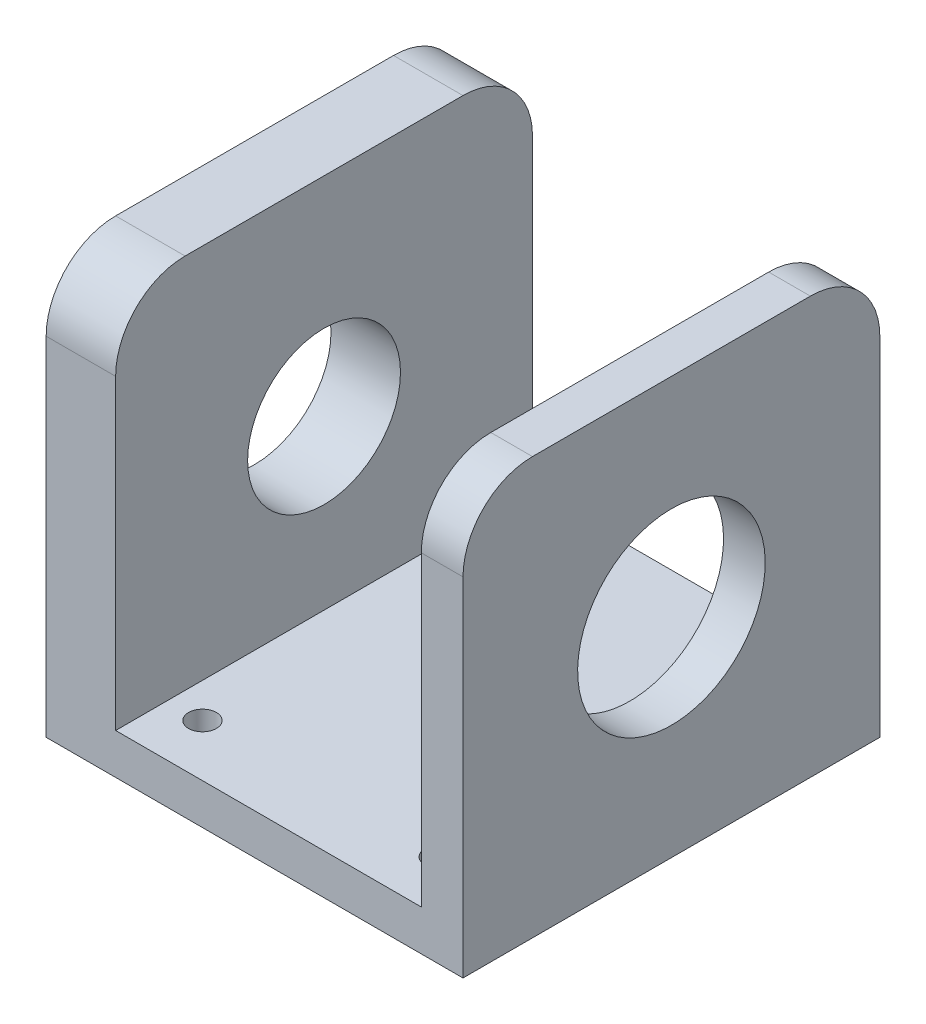
SolidWorks part; units mm, degrees
ref_plane "Front Plane" through (0, 0, 0) normal (0, 0, 1) x (1, 0, 0)
ref_plane "Top Plane" through (0, 0, 0) normal (0, 1, 0) x (1, 0, 0)
ref_plane "Right Plane" through (0, 0, 0) normal (1, 0, 0) x (0, 0, -1)
sketch "Sketch1" plane through (0, 0, 0) normal (0, 0, 1) x (1, 0, 0)
  line L0 (-30, 30) -> (-30, -30)
  line L1 (-30, -30) -> (30, -30)
  line L2 (30, -30) -> (30, 30)
  line L3 (-20, 30) -> (-20, -24.1479)
  line L4 (-20, -24.1479) -> (24, -24.1479)
  line L5 (24, -24.1479) -> (24, 30)
  line L6 (-30, 30) -> (-20, 30)
  line L7 (24, 30) -> (30, 30)
  point P3 (0, -30)
  point P6 (-30, 0)
  dimension "D1" = 60
  dimension "D2" = 60
  dimension "D3" = 60
  dimension "D5" = 6
  dimension "D4" = 10
  dimension "D6" = 44
extrude "Boss-Extrude1" add sketch "Sketch1" along normal mid plane 60
sketch "Sketch2" plane through (0, 0, 0) normal (1, 0, 0) x (0, 0, -1)
  circle A0 centre (0, 0) radius 11
  dimension "D1" = 22
extrude "Cut-Extrude1" cut sketch "Sketch2" against normal blind 60
fillet "Fillet1" radius 10 4 edges at (27, 30, 30) (27, 30, -30) (-25, 30, -30) (-25, 30, 30)
sketch "Sketch3" plane through (0, -24.1479, 0) normal (0, 1, 0) x (1, 0, 0)
  line L0 (-20, -30) -> (-20, 30) construction
  line L1 (-15, -22.5) -> (19, -22.5) construction
  line L2 (-15, -22.5) -> (-15, 22.5) construction
  line L3 (-15, 22.5) -> (19, 22.5) construction
  line L4 (19, -22.5) -> (19, 22.5) construction
  line L5 (-15, -22.5) -> (19, 22.5) construction
  line L6 (-15, 22.5) -> (19, -22.5) construction
  line L8 (24, -20) -> (24, 20) construction
  circle A0 centre (-15, 22.5) radius 2
  circle A1 centre (19, 22.5) radius 2
  circle A2 centre (-15, -22.5) radius 2
  circle A3 centre (19, -22.5) radius 2
  point P0 (0, 0)
  point P10 (0, 0)
  dimension "D3" = 4
  dimension "D4" = 4
  dimension "D5" = 4
  dimension "D6" = 4
  dimension "D1" = 45
  dimension "D2" = 5
  dimension "D7" = 5
extrude "Cut-Extrude2" cut sketch "Sketch3" against normal mid plane 20
sketch "Sketch13" plane through (30, 0, 0) normal (1, 0, 0) x (0, 0, -1)
  circle A0 centre (0, 0) radius 13.5
  dimension "D1" = 27
extrude "Cut-Extrude3" cut sketch "Sketch13" against normal blind 10
